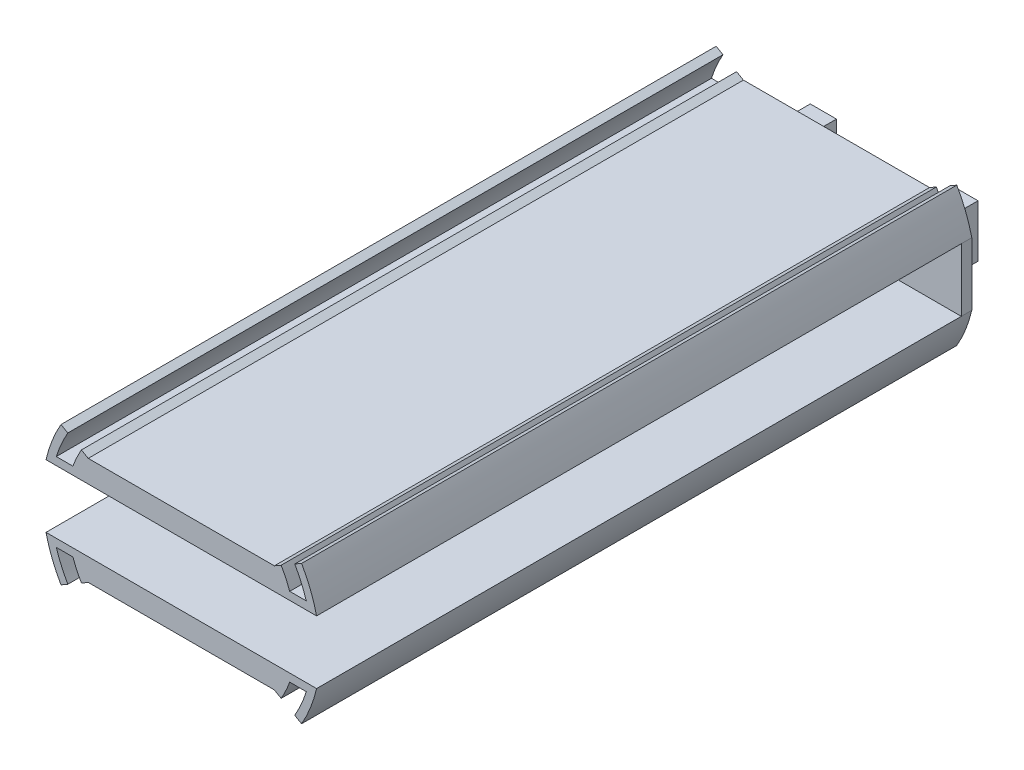
SolidWorks part; units mm, degrees
ref_plane "Front Plane" through (0, 0, 0) normal (0, 0, 1) x (1, 0, 0)
ref_plane "Top Plane" through (0, 0, 0) normal (0, 1, 0) x (1, 0, 0)
ref_plane "Right Plane" through (0, 0, 0) normal (1, 0, 0) x (0, 0, -1)
sketch "Model" plane through (0, 0, 0) normal (0, 0, 1) x (1, 0, 0)
  line L0 (-27.9688, 16.1478) -> (0, 0)
  line L1 (0, 0) -> (28.9677, -16.7245)
  line L2 (0, 0) -> (-32.9437, -19.0201)
  line L3 (0, 0) -> (27.0572, 15.6215)
  line L4 (0, 0) -> (-33.2818, 0)
  line L5 (-31.4889, 6) -> (31.9631, 6)
  line L6 (-31.4889, -6) -> (31.9631, -6)
  line L7 (-21.2132, 7.5) -> (-23.3238, 7.5)
  line L8 (23.3238, 7.5) -> (21.2132, 7.5)
  line L9 (21.2132, -7.5) -> (23.3238, -7.5)
  line L10 (-23.3238, -7.5) -> (-21.2132, -7.5)
  line L11 (-23.3238, -7.5) -> (-23.8485, -7.5)
  line L12 (-21.2132, -7.5) -> (-20.6821, -7.5)
  line L13 (21.2132, -7.5) -> (20.6821, -7.5)
  line L14 (23.3238, -7.5) -> (23.8485, -7.5)
  line L15 (21.2132, 7.5) -> (20.6821, 7.5)
  line L16 (23.3238, 7.5) -> (23.8485, 7.5)
  line L17 (-17.7535, -10.25) -> (17.7535, -10.25)
  line L18 (-17.7535, 10.25) -> (17.7535, 10.25)
  line L19 (-23.3238, 7.5) -> (-23.8485, 7.5)
  line L20 (-21.2132, 7.5) -> (-20.6821, 7.5)
  circle A0 centre (0, 0) radius 20.5
  circle A1 centre (0, 0) radius 26.5
  circle A2 centre (0, 0) radius 22
  circle A3 centre (0, 0) radius 25
  arc A5 (23.3238, 7.5) -> (23.3238, -7.5) centre (0, 0) ccw
  arc A6 (21.2132, 7.5) -> (21.2132, -7.5) centre (0, 0) ccw
extrude "Boss-Extrude2" add sketch "Model" along normal blind 125 contours A3 L5 A1 L3 | L5 A3 L16 L8 L15 A2 | L5 A2 L3 A0 | L5 A0 L3 | L18 L0 L5 L3 | L0 A2 L5 A0 | A6 L7 A5 L5 | A5 L19 A3 L5 | L20 A6 L5 A2 | A3 L0 A1 L5 | L0 A0 L5 | A3 L6 A1 L2 | A5 L6 A3 L11 | A6 L6 A5 L10 | L6 A6 L12 A2 | L6 A2 L2 A0 | L6 A0 L2 | L2 L17 L1 L6 | L1 A0 L6 | L1 A2 L6 A0 | L14 A3 L6 A2 L13 L9 | A3 L1 A1 L6
sketch "Sketch2" plane through (0, 6, 0) normal (0, -1, 0) x (1, 0, 0)
  line L0 (25.8118, 125) -> (25.8118, 0) construction
  line L1 (-25.8118, 0) -> (25.8118, 0)
  line L2 (-25.8118, 0) -> (-25.8118, 2)
  line L3 (-25.8118, 2) -> (25.8118, 2)
  line L4 (25.8118, 0) -> (25.8118, 2)
  dimension "D1" = 2
extrude "Boss-Extrude3" add sketch "Sketch2" along normal up to vertex
sketch "Sketch3" plane through (0, 0, 0) normal (0, 0, -1) x (-1, 0, 0)
  line L0 (0, 14.446) -> (0, -16.1393) construction
  line L1 (0, -8.3078) -> (-11, -8.3078)
  line L2 (16, -8.3078) -> (16, 1.6922)
  line L3 (-11, -8.3078) -> (-16, -8.3078)
  line L4 (-11, -8.3078) -> (-11, 1.6922)
  line L5 (-11, 1.6922) -> (-16, 1.6922)
  line L6 (-16, -8.3078) -> (-16, 1.6922)
  line L7 (11, 1.6922) -> (16, 1.6922)
  line L8 (11, -8.3078) -> (11, 1.6922)
  line L9 (11, -8.3078) -> (16, -8.3078)
  dimension "D1" = 11
  dimension "D2" = 10
  dimension "D3" = 5
extrude "Boss-Extrude4" add sketch "Sketch3" along normal blind 11 contours L6 L3 L4 L5 | L8 L9 L2 L7
sketch "Sketch4" plane through (0, 1.6922, 0) normal (0, 1, 0) x (1, 0, 0)
  line L0 (0, 0) -> (0, 16.463) construction
  line L1 (11, 11) -> (11, 0) construction
  line L2 (11, 11) -> (16, 11) construction
  circle A0 centre (14, 5.5) radius 1.3
  circle A1 centre (-14, 5.5) radius 1.3
  dimension "D1" = 2.6
  dimension "D2" = 3
  dimension "D3" = 5.5
extrude "Cut-Extrude1" cut sketch "Sketch4" against normal up to next
